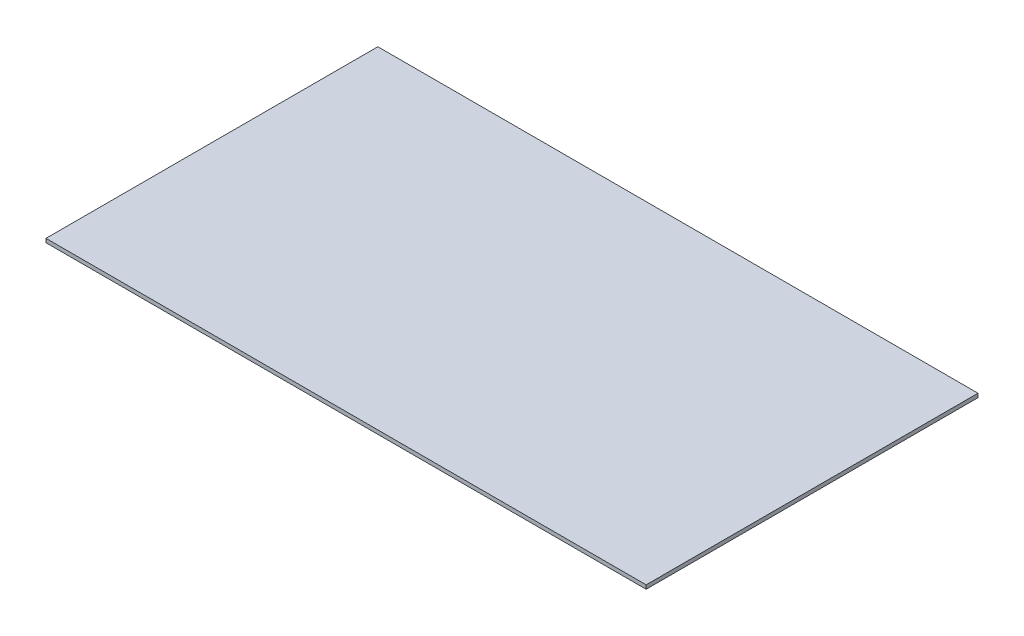
SolidWorks part; units mm, degrees
ref_plane "Front Plane" through (0, 0, 0) normal (0, 0, 1) x (1, 0, 0)
ref_plane "Top Plane" through (0, 0, 0) normal (0, 1, 0) x (1, 0, 0)
ref_plane "Right Plane" through (0, 0, 0) normal (1, 0, 0) x (0, 0, -1)
sketch "Sketch1" plane through (0, 0, 0) normal (0, 1, 0) x (1, 0, 0)
  line L1 (-128.4127, 73.6622) -> (120.7079, 73.6622)
  line L2 (-128.4127, 73.6622) -> (-128.4127, -64.0896)
  line L3 (-128.4127, -64.0896) -> (120.7079, -64.0896)
  line L4 (120.7079, 73.6622) -> (120.7079, -64.0896)
extrude "Extrude1" add sketch "Sketch1" along normal blind 1.6
